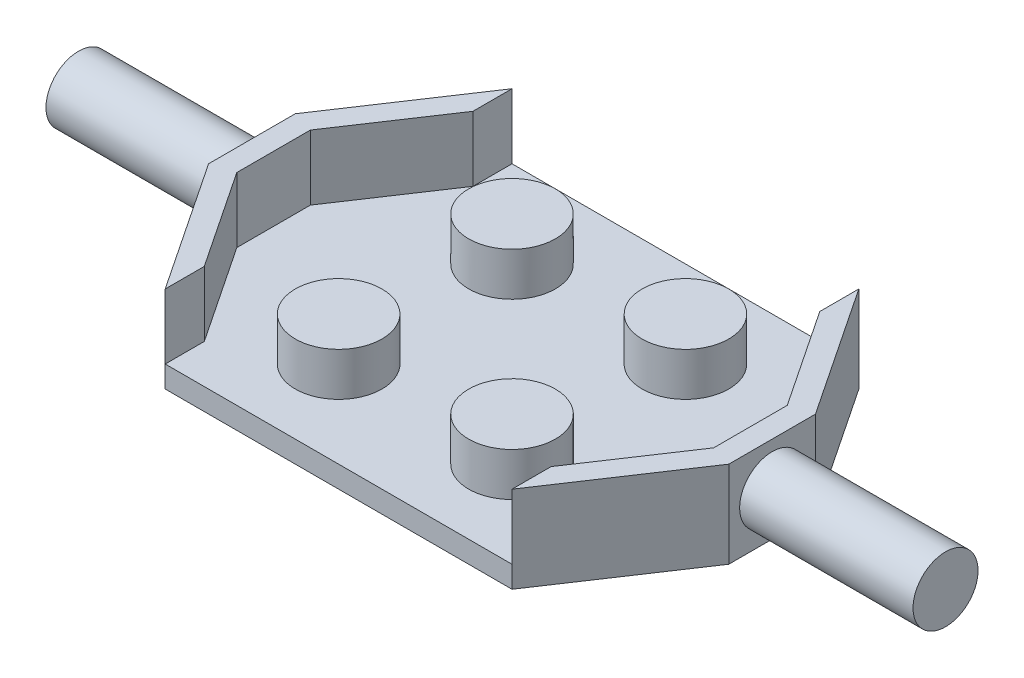
SolidWorks part; units mm, degrees
ref_plane "Front Plane" through (0, 0, 0) normal (0, 0, 1) x (1, 0, 0)
ref_plane "Top Plane" through (0, 0, 0) normal (0, 1, 0) x (1, 0, 0)
ref_plane "Right Plane" through (0, 0, 0) normal (1, 0, 0) x (0, 0, -1)
sketch "Sketch1" plane through (0, 0, 0) normal (0, 1, 0) x (1, 0, 0)
  line L0 (0, -8) -> (0, 8)
  line L1 (0, 8) -> (-8, 8)
  line L2 (0, 0) -> (-12, 0) construction
  line L3 (-12, -2) -> (-12, 2)
  line L4 (-8, 8) -> (-12, 2)
  line L5 (-8, -8) -> (-12, -2)
  line L6 (0, -8) -> (-8, -8)
  dimension "D1" = 8
  dimension "D2" = 8
  dimension "D3" = 12
  dimension "D4" = 2
extrude "Boss-Extrude1" add sketch "Sketch1" along normal blind 1
sketch "Sketch2" plane through (0, 1, 0) normal (0, 1, 0) x (1, 0, 0)
  line L0 (0, 8) -> (-8, 8) construction
  line L1 (0, -8) -> (0, 8) construction
  line L2 (-12, 0) -> (0, 0) construction
  line L3 (-12, 2) -> (-12, -2) construction
  circle A0 centre (-4, 4) radius 2
  circle A1 centre (-4, -4) radius 2
  dimension "D1" = 4
  dimension "D2" = 4
  dimension "D3" = 4
extrude "Boss-Extrude2" add sketch "Sketch2" along normal blind 2
sketch "Sketch3" plane through (0, 1, 0) normal (0, 1, 0) x (1, 0, 0)
  line L0 (-8, 6.1972) -> (-11, 1.6972)
  line L1 (-11, 1.6972) -> (-11, -1.6972)
  line L2 (-11, -1.6972) -> (-8, -6.1972)
  line L3 (-8, 8) -> (-12, 2) construction
  line L4 (-12, 2) -> (-12, -2) construction
  line L5 (-12, -2) -> (-8, -8) construction
  line L6 (-8, 8) -> (-8, 6.1972)
  line L7 (-8, -8) -> (-8, -6.1972)
  line L8 (-8, 8) -> (-12, 2)
  line L9 (-12, 2) -> (-12, -2)
  line L10 (-12, -2) -> (-8, -8)
  dimension "D1" = 1
  dimension "D2" = 1
  dimension "D3" = 1
extrude "Boss-Extrude3" add sketch "Sketch3" along normal blind 3
sketch "Sketch5" plane through (-12, 0, 0) normal (-1, 0, 0) x (0, 0, 1)
  line L0 (0, 4) -> (0, 0) construction
  line L1 (-2, 4) -> (2, 4) construction
  circle A0 centre (0, 2) radius 1.5
  dimension "D1" = 3
extrude "Boss-Extrude4" add sketch "Sketch5" along normal blind 8
mirror "Mirror1" about plane through (0, 1, 8) normal (-1, 0, 0) of "Boss-Extrude4", "Boss-Extrude3", "Boss-Extrude2", "Boss-Extrude1"
